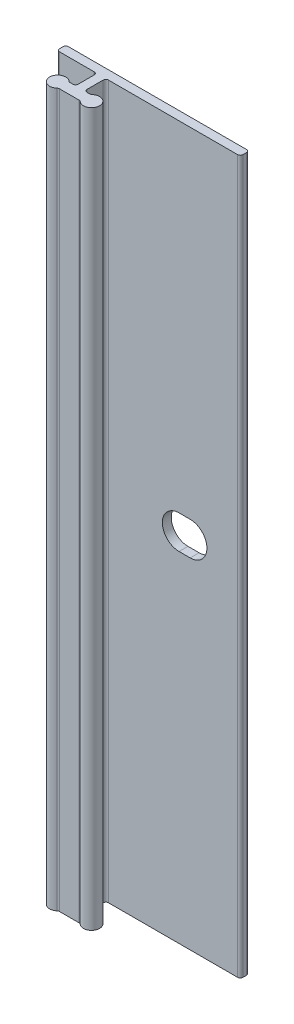
SolidWorks part; units mm, degrees
material "6463-T6"
ref_plane "Front Plane" through (0, 0, 0) normal (0, 0, 1) x (1, 0, 0)
ref_plane "Top Plane" through (0, 0, 0) normal (0, 1, 0) x (1, 0, 0)
ref_plane "Right Plane" through (0, 0, 0) normal (1, 0, 0) x (0, 0, -1)
sketch "Sketch2" plane through (0, 0, 0) normal (0, 1, 0) x (1, 0, 0)
  line L0 (0, 7.209) -> (0, -15.6826) construction
  line L16 (-5.969, 0) -> (19.431, 0)
  line L18 (19.812, -0.381) -> (19.812, -0.889)
  line L19 (19.431, -1.27) -> (1.016, -1.27)
  line L20 (0.635, -1.651) -> (0.635, -3.937)
  line L52 (-0.635, -1.651) -> (-0.635, -3.937)
  line L53 (-8.0148, -5.08) -> (8.0148, -5.08) construction
  line L54 (-1.405, -4.318) -> (-1.016, -4.318)
  line L55 (-1.405, -5.842) -> (1.405, -5.842)
  line L56 (1.016, -4.318) -> (1.405, -4.318)
  line L57 (-1.016, -1.27) -> (-5.969, -1.27)
  line L58 (-6.35, -0.889) -> (-6.35, -0.381)
  arc A11 (19.431, 0) -> (19.812, -0.381) centre (19.431, -0.381) cw
  arc A12 (19.812, -0.889) -> (19.431, -1.27) centre (19.431, -0.889) cw
  arc A19 (1.016, -1.27) -> (0.635, -1.651) centre (1.016, -1.651) ccw
  arc A20 (-1.657, -4.2227) -> (-1.657, -5.9373) centre (-2.413, -5.08) ccw
  arc A21 (1.657, -5.9373) -> (1.657, -4.2227) centre (2.413, -5.08) ccw
  arc A22 (0.635, -3.937) -> (1.016, -4.318) centre (1.016, -3.937) ccw
  arc A23 (-0.635, -3.937) -> (-1.016, -4.318) centre (-1.016, -3.937) cw
  arc A24 (1.405, -5.842) -> (1.657, -5.9373) centre (1.405, -6.223) cw
  arc A25 (1.657, -4.2227) -> (1.405, -4.318) centre (1.405, -3.937) cw
  arc A26 (-1.405, -5.842) -> (-1.657, -5.9373) centre (-1.405, -6.223) ccw
  arc A27 (-1.405, -4.318) -> (-1.657, -4.2227) centre (-1.405, -3.937) cw
  arc A28 (-6.35, -0.381) -> (-5.969, 0) centre (-5.969, -0.381) cw
  arc A29 (-5.969, -1.27) -> (-6.35, -0.889) centre (-5.969, -0.889) cw
  arc A30 (-1.016, -1.27) -> (-0.635, -1.651) centre (-1.016, -1.651) cw
  point P7 (0, -5.08)
  point P16 (19.812, 0)
  point P19 (19.812, -1.27)
  point P22 (0.635, -1.27)
  point P30 (0.635, -4.318)
  point P36 (1.5611, -5.842)
  point P39 (1.5611, -4.318)
  point P42 (-1.5611, -5.842)
  point P45 (-1.5611, -4.318)
  dimension "D7" = 0.381
  dimension "D6" = 2.286
  dimension "D10" = 1.524
  dimension "D11" = 19.812
  dimension "D12" = 6.35
  dimension "D2" = 1.27
  dimension "D3" = 1.27
  dimension "D4" = 0.635
  dimension "D5" = 5.08
  dimension "D8" = 2.413
  dimension "D9" = 2.413
extrude "Boss-Extrude1" add sketch "Sketch2" along normal mid plane 101.6
sketch "Sketch3" plane through (0, 0, 1.27) normal (0, 0, 1) x (1, 0, 0)
  line L0 (0, 0) -> (19.812, 0) construction
  line L1 (19.812, 50.8) -> (19.812, -50.8) construction
  line L2 (11.0808, 0) -> (12.6683, 0) construction
  line L3 (11.0808, 2.3813) -> (12.6683, 2.3813)
  line L4 (11.0808, -2.3813) -> (12.6683, -2.3812)
  arc A0 (11.0808, 2.3813) -> (11.0808, -2.3813) centre (11.0808, 0) ccw
  arc A1 (12.6683, -2.3812) -> (12.6683, 2.3813) centre (12.6683, 0) ccw
  point P7 (11.8745, 0)
  dimension "D1" = 4.7625
  dimension "D2" = 6.35
  dimension "D3" = 7.9375
extrude "Cut-Extrude1" cut sketch "Sketch3" against normal through all
